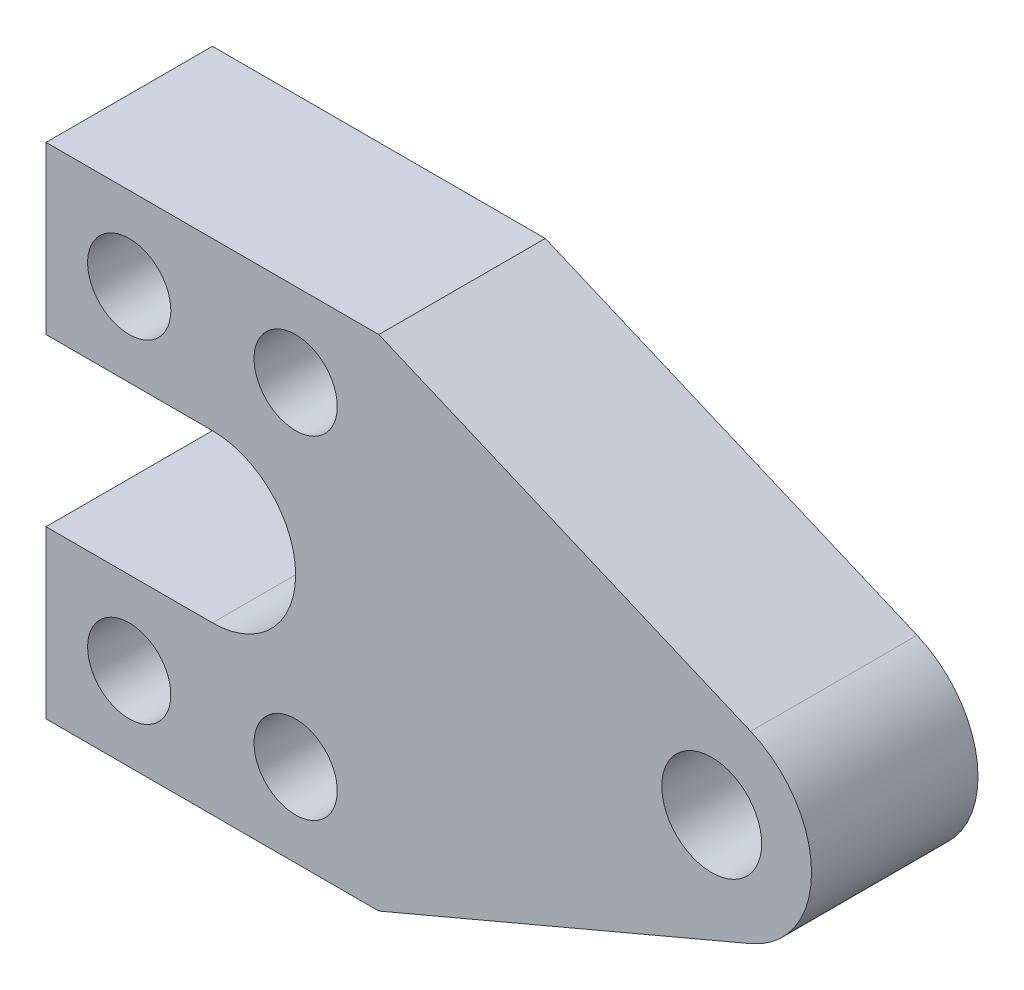
SolidWorks part; units mm, degrees
ref_plane "Front Plane" through (0, 0, 0) normal (0, 0, 1) x (1, 0, 0)
ref_plane "Top Plane" through (0, 0, 0) normal (0, 1, 0) x (1, 0, 0)
ref_plane "Right Plane" through (0, 0, 0) normal (1, 0, 0) x (0, 0, -1)
sketch "Sketch1" plane through (0, 0, 0) normal (0, 0, 1) x (1, 0, 0)
  line L0 (0, 0) -> (20.3943, 0) construction
  line L1 (0, 10) -> (20, 10)
  line L2 (0, 10) -> (0, 30)
  line L3 (0, 30) -> (40, 30)
  line L4 (40, 30) -> (84.6856, 11.0474)
  line L5 (40, -30) -> (84.6856, -11.0474)
  line L6 (0, -30) -> (40, -30)
  line L7 (0, -10) -> (0, -30)
  line L8 (0, -10) -> (20, -10)
  arc A0 (20, 10) -> (20, -10) centre (20, 0) cw
  circle A1 centre (80, 0) radius 6
  arc A2 (84.6856, -11.0474) -> (84.6856, 11.0474) centre (80, 0) ccw
  circle A3 centre (10, 20) radius 5
  circle A4 centre (30, 20) radius 5
  circle A5 centre (30, -20) radius 5
  circle A6 centre (10, -20) radius 5
  point P18 (0, 0)
  point P19 (20, 0)
  dimension "D1" = 12
  dimension "D2" = 6
  dimension "D7" = 10
  dimension "D8" = 10
  dimension "D9" = 10
  dimension "D3" = 60
  dimension "D4" = 10
  dimension "D5" = 10
  dimension "D6" = 20
  dimension "D10" = 80
  dimension "D11" = 40
  dimension "D12" = 20
extrude "Boss-Extrude1" add sketch "Sketch1" along normal blind 20
